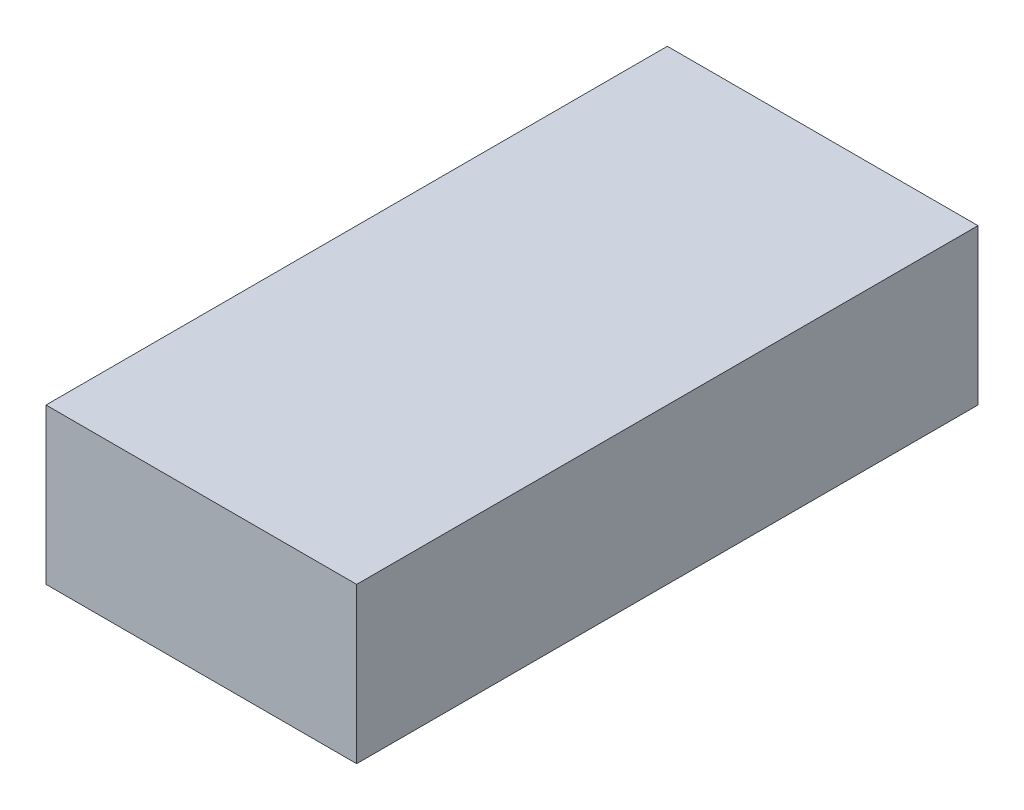
SolidWorks part; units mm, degrees
ref_plane "Front Plane" through (0, 0, 0) normal (0, 0, 1) x (1, 0, 0)
ref_plane "Top Plane" through (0, 0, 0) normal (0, 1, 0) x (1, 0, 0)
ref_plane "Right Plane" through (0, 0, 0) normal (1, 0, 0) x (0, 0, -1)
sketch "Sketch1" plane through (0, 0, 0) normal (0, 0, 1) x (1, 0, 0)
  line L1 (-5, -2.5) -> (5, -2.5)
  line L2 (-5, -2.5) -> (-5, 2.5)
  line L3 (-5, 2.5) -> (5, 2.5)
  line L4 (5, -2.5) -> (5, 2.5)
  line L5 (-5, -2.5) -> (5, 2.5) construction
  line L6 (-5, 2.5) -> (5, -2.5) construction
  point P0 (0, 0)
  dimension "D1" = 5
  dimension "10" = 10
extrude "Boss-Extrude1" add sketch "Sketch1" along normal blind 20
